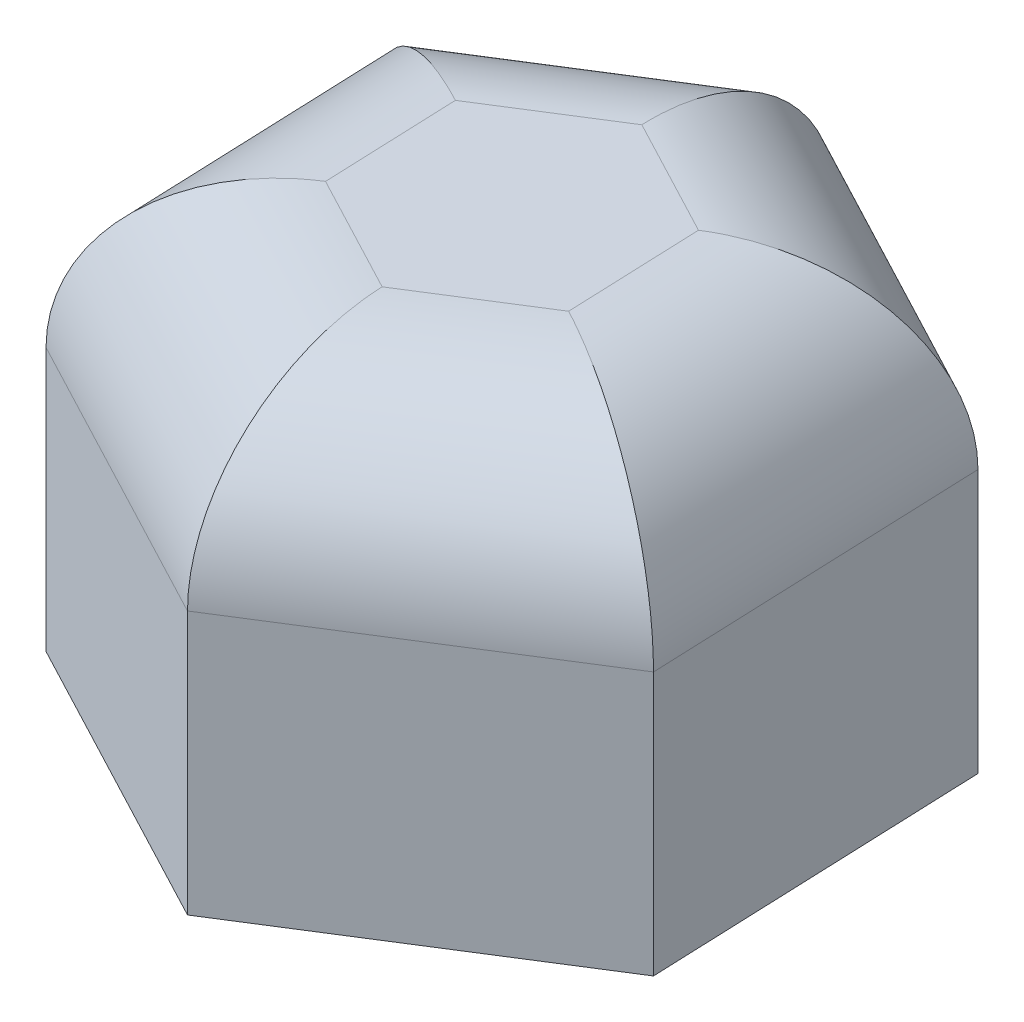
SolidWorks part; units mm, degrees
ref_plane "Спереди" through (0, 0, 0) normal (0, 0, 1) x (1, 0, 0)
ref_plane "Сверху" through (0, 0, 0) normal (0, 1, 0) x (1, 0, 0)
ref_plane "Справа" through (0, 0, 0) normal (1, 0, 0) x (0, 0, -1)
sketch "Sketch1" plane through (0, 0, 0) normal (0, 1, 0) x (1, 0, 0)
  line L1 (-6.8128, 3.5883) -> (-6.5139, -4.1059)
  line L2 (-6.5139, -4.1059) -> (0.2988, -7.6942)
  line L3 (0.2988, -7.6942) -> (6.8128, -3.5883)
  line L4 (6.8128, -3.5883) -> (6.5139, 4.1059)
  line L5 (6.5139, 4.1059) -> (-0.2988, 7.6942)
  line L6 (-0.2988, 7.6942) -> (-6.8128, 3.5883)
  circle A0 centre (0, 0) radius 7.7 construction
  dimension "D1" = 15.4
extrude "Boss-Extrude1" add sketch "Sketch1" along normal blind 10
fillet "Fillet1" radius 4 6 edges at (3.1076, 10, -5.9001) (6.6634, 10, -0.2588) (3.5558, 10, 5.6412) (-3.1076, 10, 5.9001) (-6.6634, 10, 0.2588) (-3.5558, 10, -5.6412)
sketch "Sketch2" plane through (0, 0, 0) normal (0, -1, 0) x (1, 0, 0)
  circle A0 centre (0, 0) radius 4.1
  dimension "D1" = 8.2
extrude "Cut-Extrude1" cut sketch "Sketch2" against normal blind 8
